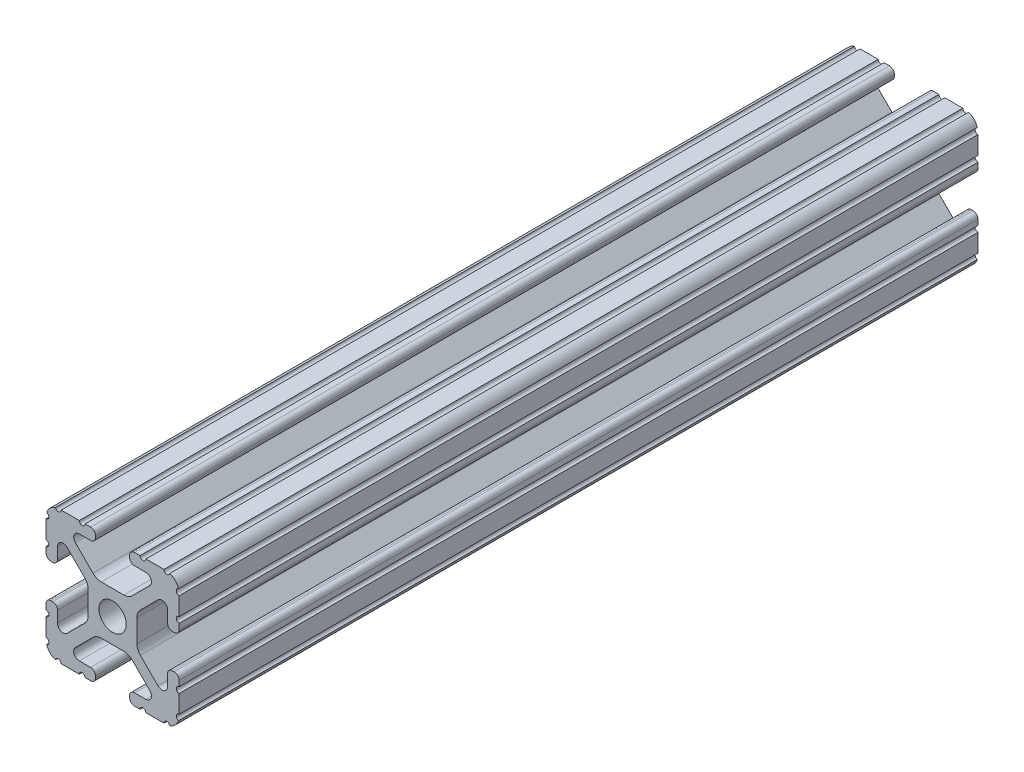
SolidWorks part; units mm, degrees
ref_plane "Front Plane" through (0, 0, 0) normal (0, 0, 1) x (1, 0, 0)
ref_plane "Top Plane" through (0, 0, 0) normal (0, 1, 0) x (1, 0, 0)
ref_plane "Right Plane" through (0, 0, 0) normal (1, 0, 0) x (0, 0, -1)
sketch "Sketch2" plane through (0, 0, 0) normal (0, 0, 1) x (1, 0, 0)
  line L0 (0, 12.7) -> (0, -12.7) construction
  line L1 (-12.7, 0) -> (12.7, 0) construction
  line L2 (3.2512, -12.7) -> (12.7, -12.7)
  line L3 (12.7, -12.7) -> (12.7, -3.2512)
  line L4 (3.2512, -12.7) -> (3.2512, -10.4902)
  line L5 (3.2512, -10.4902) -> (8.9276, -10.4902)
  line L6 (8.9276, -10.4902) -> (3.0856, -4.6482)
  line L7 (0, 0) -> (12.7, -12.7) construction
  line L8 (12.7, -3.2512) -> (10.4902, -3.2512)
  line L9 (10.4902, -3.2512) -> (10.4902, -8.9276)
  line L10 (10.4902, -8.9276) -> (4.6482, -3.0856)
  circle A0 centre (0, 0) radius 2.6035
  arc A1 (6.3485, -10.4902) -> (7.1039, -8.6665) centre (6.3485, -9.4219) ccw construction
  point P8 (0, -4.6482)
  dimension "Center Hole Diameter" = 5.207
  dimension "Rail Height" = 25.4
  dimension "Rail Width" = 25.4
  dimension "T-Slot Width" = 6.5024
  dimension "Slot Inner Width" = 14.8336
  dimension "Thickness" = 2.2098
  dimension "Slot Depth" = 5.842
  dimension "D1" = 2.2098
sketch "Sketch3" plane through (0, 0, 0) normal (1, 0, 0) x (0, 0, -1)
  line L0 (-76.2, -12.7) -> (76.2, -12.7) construction
  line L1 (-68.58, 0) -> (68.58, 0) construction
  dimension "Length" = 152.4
  dimension "D1" = 137.16
sketch "Sketch4" plane through (0, 0, 0) normal (0, 0, 1) x (1, 0, 0)
  line L0 (4.1904, -12.7) -> (10.1173, -12.7)
  line L1 (3.2512, -12.7) -> (12.7, -12.7) construction
  line L2 (3.2512, -12.7) -> (3.2512, -10.4902) construction
  line L3 (3.2512, -10.4902) -> (8.9276, -10.4902) construction
  line L4 (3.2512, -11.4294) -> (3.2512, -11.7608)
  line L5 (4.1904, -10.4902) -> (6.3485, -10.4902)
  line L6 (0, -4.6482) -> (2.164, -4.6482)
  line L7 (8.9276, -10.4902) -> (3.0856, -4.6482) construction
  line L8 (3.7373, -5.2999) -> (7.1039, -8.6665)
  line L9 (12.7, -12.7) -> (12.7, -3.2512) construction
  line L10 (10.4902, -8.9276) -> (4.6482, -3.0856) construction
  line L11 (10.4902, -3.2512) -> (10.4902, -8.9276) construction
  line L12 (10.4902, -6.3485) -> (10.4902, -4.1904)
  line L13 (12.7, -3.2512) -> (10.4902, -3.2512) construction
  line L14 (11.4294, -3.2512) -> (11.7608, -3.2512)
  line L15 (12.7, -4.1904) -> (12.7, -10.1173)
  line L16 (8.6665, -7.1039) -> (5.2999, -3.7373)
  line L17 (4.6482, 0) -> (4.6482, -2.164)
  line L18 (-12.7, 0) -> (12.7, 0) construction
  line L19 (0, -4.6482) -> (0, -2.6035)
  line L20 (0, 12.7) -> (0, -12.7) construction
  line L21 (4.6482, 0) -> (2.6035, 0)
  arc A0 (3.2512, -11.7608) -> (4.1904, -12.7) centre (4.1904, -11.7608) ccw
  arc A2 (3.2512, -11.4294) -> (4.1904, -10.4902) centre (4.1904, -11.4294) cw
  arc A3 (6.3485, -10.4902) -> (7.1039, -8.6665) centre (6.3485, -9.4219) ccw
  arc A4 (2.164, -4.6482) -> (3.7373, -5.2999) centre (2.164, -6.8732) cw
  arc A5 (10.1173, -12.7) -> (12.7, -10.1173) centre (10.1173, -10.1173) ccw
  arc A6 (8.6665, -7.1039) -> (10.4902, -6.3485) centre (9.4219, -6.3485) ccw
  arc A7 (10.4902, -4.1904) -> (11.4294, -3.2512) centre (11.4294, -4.1904) cw
  arc A8 (11.7608, -3.2512) -> (12.7, -4.1904) centre (11.7608, -4.1904) cw
  arc A9 (5.2999, -3.7373) -> (4.6482, -2.164) centre (6.8732, -2.164) cw
  circle A10 centre (0, 0) radius 2.6035 construction
  arc A11 (0, -2.6035) -> (2.6035, 0) centre (0, 0) ccw
  dimension "D1" = 2.5827
  dimension "D2" = 2.225
  dimension "D3" = 0.9392
extrude "Boss-Extrude1" add sketch "Sketch4" along normal mid plane 152.4
sketch "Sketch5" plane through (0, 0, 0) normal (0, 0, 1) x (1, 0, 0)
  line L0 (3.2512, -12.7) -> (12.7, -12.7) construction
  line L1 (4.1904, -10.4902) -> (6.3485, -10.4902) construction
  line L3 (0, 0) -> (12.7, -12.7) construction
  line L4 (6.3485, -10.4902) -> (6.3485, -12.7) construction
  line L5 (8.9276, -10.4902) -> (3.0856, -4.6482) construction
  circle A0 centre (10.3562, -12.7) radius 0.5524
  circle A1 centre (5.796, -12.7) radius 0.5524
  circle A2 centre (12.7, -10.3562) radius 0.5524
  circle A3 centre (12.7, -5.796) radius 0.5524
  point P10 (5.2694, -10.4902)
  point P12 (9.4219, -6.3485)
  dimension "D1" = 1.1049
extrude "Cut-Extrude1" cut sketch "Sketch5" against normal through all both and the other way through all
mirror "Mirror1" about plane through (0, 0, 0) normal (1, 0, 0) of bodies 137 134
mirror "Mirror2" about plane through (0, 0, 0) normal (0, 1, 0) of bodies 135
sketch "Sketch6" plane through (0, 0, 0) normal (0, 1, 0) x (1, 0, 0)
  line L0 (0, 76.2) -> (0, 63.5) construction
  line L1 (0, -76.2) -> (0, -63.5) construction
  line L4 (2.164, 76.2) -> (-2.164, 76.2)
  line L5 (-2.164, 76.2) -> (-2.164, -76.2)
  line L6 (-2.164, -76.2) -> (2.164, -76.2)
  line L7 (2.164, -76.2) -> (2.164, 76.2)
  line L8 (2.164, 76.2) -> (-2.164, 76.2) construction
  line L9 (-2.164, 76.2) -> (-2.164, -76.2) construction
  line L10 (-2.164, -76.2) -> (2.164, -76.2) construction
  line L11 (2.164, -76.2) -> (2.164, 76.2) construction
  circle A0 centre (0, -63.5) radius 2.555
  circle A1 centre (0, 63.5) radius 2.555
  dimension "D2" = 12.7
  dimension "D3" = 5.11
  dimension "D4" = 127
  dimension "D1" = 0
extrude "Cut-Extrude2" cut sketch "Sketch6" against normal through all both and the other way through all
equation "\"D1@Boss-Extrude1\"=\"Length@Sketch3\""
equation "\"D1@Sketch2\"=\"Thickness@Sketch2\""
equation "\"D2@Sketch4\"=\"Slot Inner Width@Sketch2\"*0.15"
equation "\"D1@Sketch4\"=\"D3@Sketch4\"*2.75"
equation "\"D3@Sketch4\"=\"Thickness@Sketch2\"*0.425"
equation "\"D1@Sketch5\"=\"Thickness@Sketch2\"*0.5"
equation "\"D1@Sketch3\"=\"Length@Sketch3\"*0.9"
